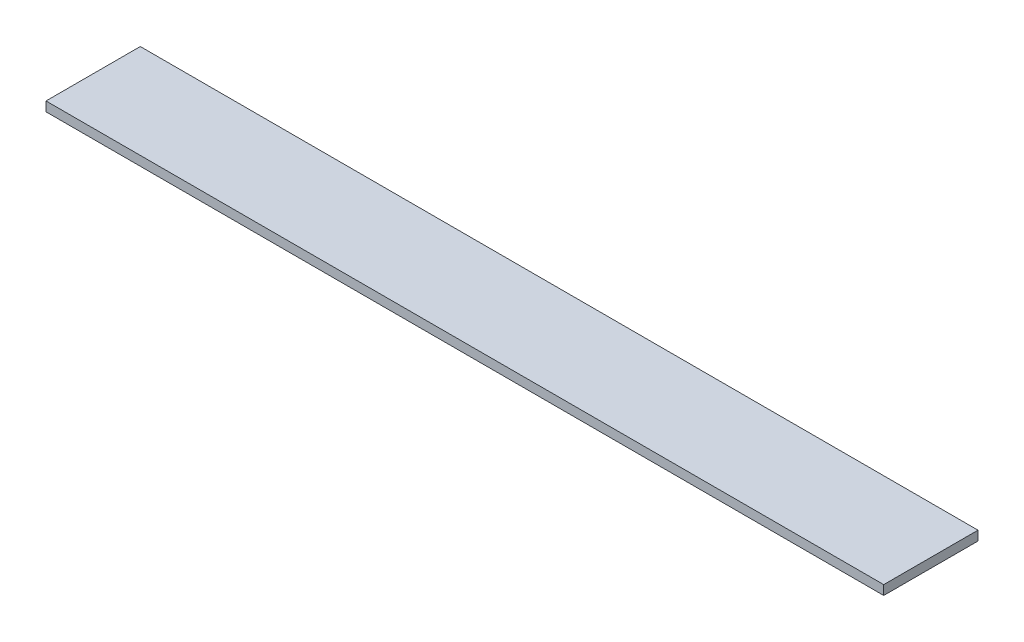
SolidWorks part; units mm, degrees
ref_plane "Front Plane" through (0, 0, 0) normal (0, 0, 1) x (1, 0, 0)
ref_plane "Top Plane" through (0, 0, 0) normal (0, 1, 0) x (1, 0, 0)
ref_plane "Right Plane" through (0, 0, 0) normal (1, 0, 0) x (0, 0, -1)
sketch "Sketch1" plane through (0, 0, 0) normal (0, 1, 0) x (1, 0, 0)
  line L0 (-444.265, 50) -> (444.265, -50) construction
  line L1 (-444.265, 50) -> (444.265, 50)
  line L2 (-444.265, 50) -> (-444.265, -50)
  line L3 (-444.265, -50) -> (444.265, -50)
  line L4 (444.265, 50) -> (444.265, -50)
  dimension "D1" = 888.53
  dimension "D2" = 100
extrude "Boss-Extrude1" add sketch "Sketch1" along normal blind 10
